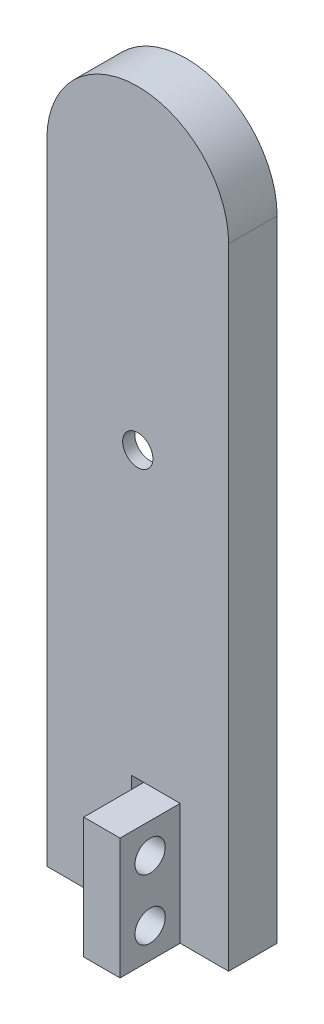
SolidWorks part; units mm, degrees
ref_plane "前基準面" through (0, 0, 0) normal (0, 0, 1) x (1, 0, 0)
ref_plane "上基準面" through (0, 0, 0) normal (0, 1, 0) x (1, 0, 0)
ref_plane "右基準面" through (0, 0, 0) normal (1, 0, 0) x (0, 0, -1)
sketch "草圖1" plane through (0, 0, 0) normal (0, 0, 1) x (1, 0, 0)
  line L0 (0, 0) -> (0, 4.6483) construction
  line L1 (7.5, 0) -> (7.5, 52)
  line L2 (7.5, 0) -> (-7.5, 0)
  line L3 (-7.5, 0) -> (-7.5, 52)
  arc A0 (7.5, 52) -> (-7.5, 52) centre (0, 52) ccw
  dimension "D1" = 7.5
  dimension "D2" = 52
extrude "填料-伸長1" add sketch "草圖1" along normal blind 4
sketch "草圖3" plane through (0, 0, 0) normal (0, 0, 1) x (1, 0, 0)
  line L0 (0, 0) -> (0, 15.7412) construction
  line L1 (7.5, 52) -> (-7.5, 52) construction
  line L2 (7.5, 15) -> (-7.5, 15) construction
  line L3 (7.5, 0) -> (7.5, 52) construction
  line L4 (-7.5, 52) -> (-7.5, 0) construction
  line L5 (-7.5, 0) -> (7.5, 0) construction
  line L6 (7.5, 33.5) -> (5, 33.5) construction
  line L7 (5, 33.5) -> (2.4679, 17.8421)
  line L8 (5, 33.5) -> (2.5, 48.7588)
  line L9 (-2.5, 48.7588) -> (-5, 33.5)
  line L10 (-5, 33.5) -> (-2.5, 18.2412)
  line L11 (0, 51.2588) -> (0, 59.5) construction
  line L12 (-5, 33.5) -> (-7.5, 33.5) construction
  arc A0 (7.5, 52) -> (-7.5, 52) centre (0, 52) ccw construction
  arc A1 (-4.7386, 35.0956) -> (-4.7386, 31.9044) centre (0, 33.5) ccw
  arc A2 (-2.5, 18.2412) -> (2.4679, 17.8421) centre (0, 18.2412) ccw
  arc A3 (-2.5, 48.7588) -> (2.5, 48.7588) centre (0, 48.7588) cw
  arc A4 (4.7452, 31.9241) -> (4.7386, 35.0956) centre (0, 33.5) ccw
  dimension "D4" = 10
  dimension "D1" = 15
  dimension "D2" = 37
  dimension "D3" = 18.5
extrude "除料-伸長1" cut sketch "草圖3" along normal blind 3 contours A3 L9 L10 A2 L7 L8
sketch "草圖5" plane through (0, 0, 0) normal (0, 0, 1) x (1, 0, 0)
  line L0 (5, 33.5) -> (-5, 33.5) construction
  circle A0 centre (0, 33.5) radius 1.25
  dimension "D1" = 2.5
extrude "除料-伸長2" cut sketch "草圖5" along normal blind 12.4
sketch "草圖6" plane through (0, 0, 0) normal (0, 0, 1) x (1, 0, 0)
  line L0 (0, 0) -> (0, 56.6939) construction
  line L1 (0.5, 0) -> (0.5, 10)
  line L2 (7.5, 0) -> (-7.5, 0) construction
  line L3 (0.5, 10) -> (-0.5, 10)
  line L4 (0.5, 0) -> (-0.5, 0)
  line L5 (-0.5, 0) -> (-0.5, 10)
  point P10 (0, 10)
  dimension "D1" = 0.5
  dimension "D2" = 10
extrude "除料-伸長3" cut sketch "草圖6" along normal blind 16.3
ref_plane "平面1" through (0.5, 0, 0) normal (1, 0, 0) x (0, 0, -1)
sketch "草圖9" plane through (0.5, 0, 0) normal (1, 0, 0) x (0, 0, -1)
  line L0 (-4, 0) -> (0, 0) construction
  line L1 (-8.9618, 10) -> (-3.9618, 10)
  line L2 (-8.9618, 10) -> (-8.9618, 0)
  line L3 (-8.9618, 0) -> (-3.9618, 0)
  line L4 (-3.9618, 10) -> (-3.9618, 0)
  dimension "D1" = 5
  dimension "D2" = 10
extrude "填料-伸長4" add sketch "草圖9" along normal blind 3
sketch "草圖10" plane through (0.5, 0, 0) normal (1, 0, 0) x (0, 0, -1)
  line L0 (-8.9618, 5) -> (-4, 5) construction
  line L1 (-8.9618, 10) -> (-8.9618, 0) construction
  line L2 (-4, 0) -> (-4, 10) construction
  line L3 (-6.4809, 10) -> (-6.4809, 0) construction
  line L4 (-4, 10) -> (-8.9618, 10) construction
  line L5 (-8.9618, 0) -> (-4, 0) construction
  circle A0 centre (-6.4809, 7.5) radius 1.25
  circle A1 centre (-6.4809, 2.5) radius 1.25
  dimension "D2" = 2.5
  dimension "D1" = 2.5
extrude "除料-伸長4" cut sketch "草圖10" along normal blind 5.1
